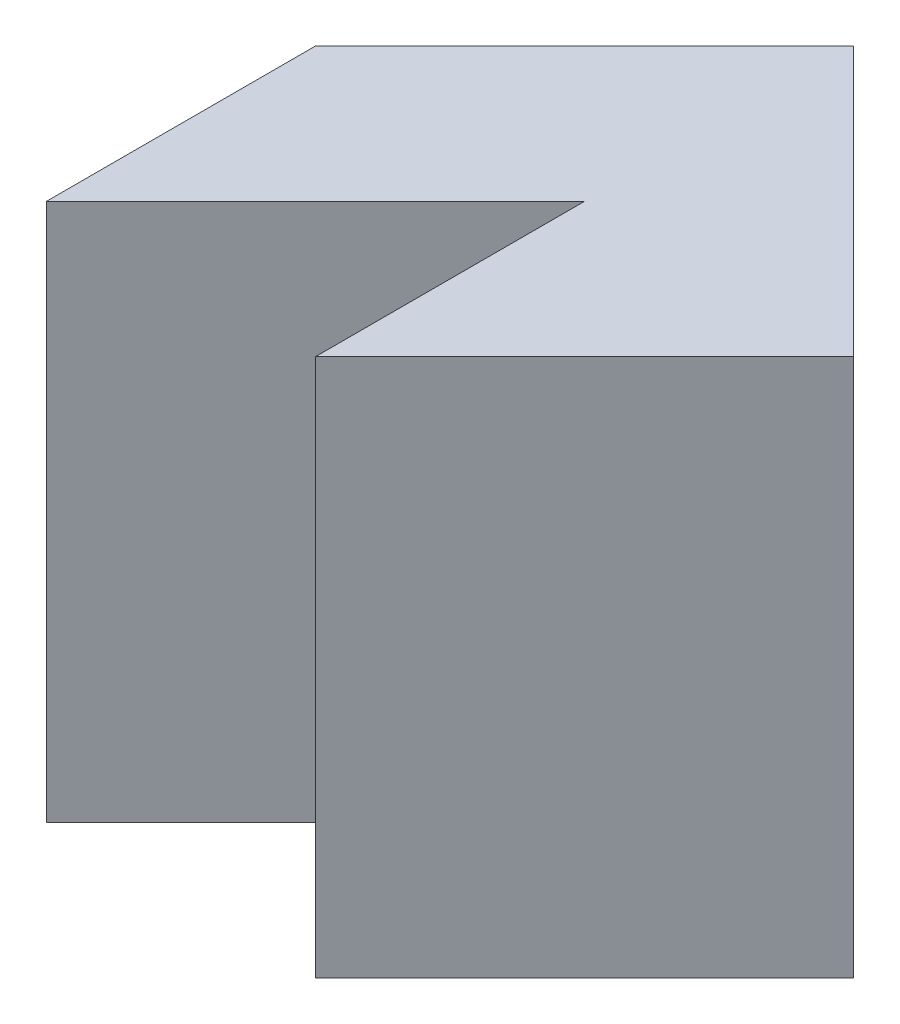
SolidWorks part; units mm, degrees
ref_plane "Front Plane" through (0, 0, 0) normal (0, 0, 1) x (1, 0, 0)
ref_plane "Top Plane" through (0, 0, 0) normal (0, 1, 0) x (1, 0, 0)
ref_plane "Right Plane" through (0, 0, 0) normal (1, 0, 0) x (0, 0, -1)
sketch "Sketch2" plane through (0, 0, 0) normal (0, 1, 0) x (1, 0, 0)
  line L0 (0, 0) -> (0, 2)
  line L1 (0, 2) -> (-2, 0)
  line L2 (-2, 0) -> (-2, 2)
  line L3 (-2, 2) -> (0, 4)
  line L4 (0, 4) -> (2, 2)
  line L5 (2, 2) -> (0, 0)
  dimension "D1" = 2
  dimension "D2" = 2
  dimension "D3" = 2
  dimension "D4" = 2
  dimension "D5" = 2
  dimension "D6" = 2
  dimension "D7" = 2
extrude "Boss-Extrude2" add sketch "Sketch2" along normal blind 4
